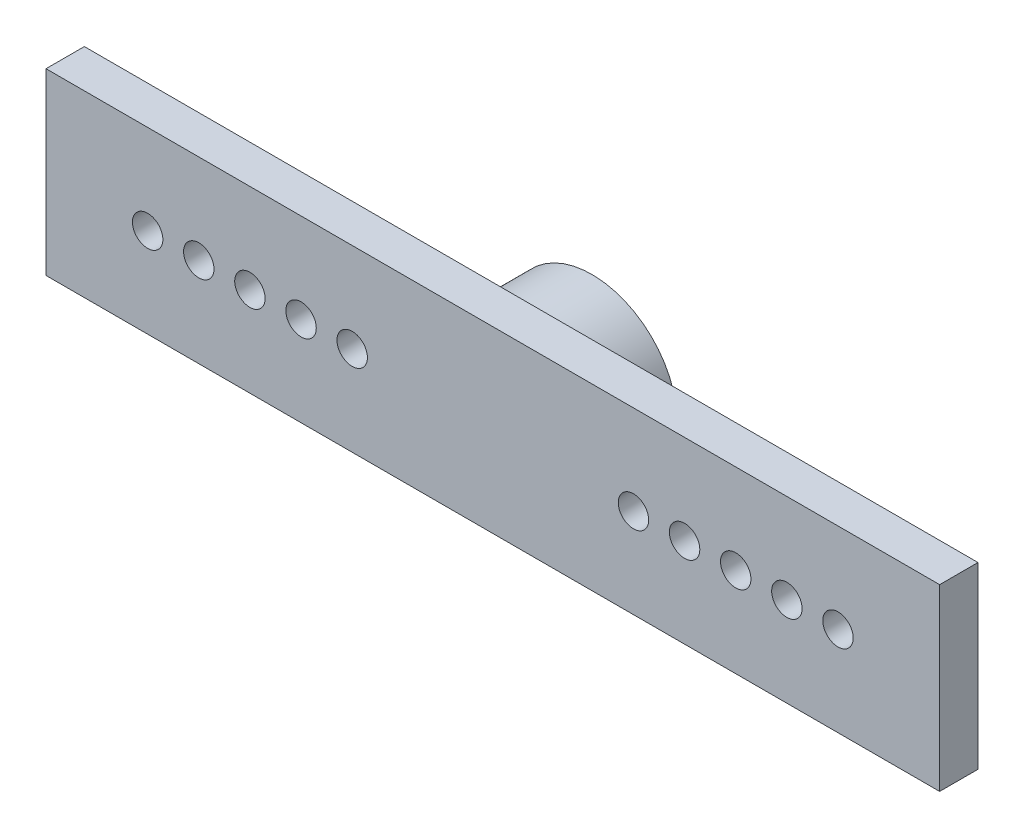
SolidWorks part; units mm, degrees
ref_plane "Front Plane" through (0, 0, 0) normal (0, 0, 1) x (1, 0, 0)
ref_plane "Top Plane" through (0, 0, 0) normal (0, 1, 0) x (1, 0, 0)
ref_plane "Right Plane" through (0, 0, 0) normal (1, 0, 0) x (0, 0, -1)
sketch "Sketch1" plane through (0, 0, 0) normal (0, 0, 1) x (1, 0, 0)
  line L1 (-22.1938, -4.4478) -> (22.1938, -4.4478)
  line L2 (-22.1938, -4.4478) -> (-22.1938, 4.4478)
  line L3 (-22.1938, 4.4478) -> (22.1938, 4.4478)
  line L4 (22.1938, -4.4478) -> (22.1938, 4.4478)
  line L5 (-22.1938, -4.4478) -> (22.1938, 4.4478) construction
  line L6 (-22.1938, 4.4478) -> (22.1938, -4.4478) construction
  point P0 (0, 0)
extrude "Extrude1" add sketch "Sketch1" along normal blind 1.905
sketch "Sketch2" plane through (0, 0, 0) normal (0, 0, -1) x (-1, 0, 0)
  circle A0 centre (0, 0) radius 4.2291
  circle A1 centre (0, 0) radius 2.9718
extrude "Extrude2" add sketch "Sketch2" along normal blind 3.0226
sketch "Sketch3" plane through (0, 0, 1.905) normal (0, 0, 1) x (1, 0, 0)
  line L0 (0, 0) -> (6.985, 0) construction
  line L1 (0, 0) -> (0, 4.4478) construction
  line L2 (22.1938, 4.4478) -> (-22.1938, 4.4478) construction
hole_wizard "#53 (0.0595) Diameter Hole1" positions "3DSketch1" profile "Sketch4" hole size "#53" standard "Ansi Inch"
sketch3d "3DSketch1"
  point P0 (6.985, 0, 1.905)
sketch "Sketch4" plane through (6.985, 0, 1.905) normal (1, 0, 0) x (0, -1, 0)
  line L0 (0, 0) -> (0, 5.534)
  line L1 (0, 5.534) -> (0.7556, 5.08)
  line L2 (0.7556, 5.08) -> (0.7556, 0)
  line L5 (0.7556, 0) -> (0, 0)
  line L10 (0, 5.534) -> (-0.7557, 5.08) construction
  line L11 (0, -6.35) -> (0, 107.95) construction
  dimension "Hole Dia." = 1.5113
  dimension "Hole Depth" = 5.08
  dimension "Drill Angle" = 118
pattern_linear "LPattern2" count 5 spacing 2.54 along (1, 0, 0) of "#53 (0.0595) Diameter Hole1"
pattern_circular "CirPattern2" count 2 over 360 about axis through (0, 0, 0) along (0, 0, 1) of "LPattern2", "#53 (0.0595) Diameter Hole1"
